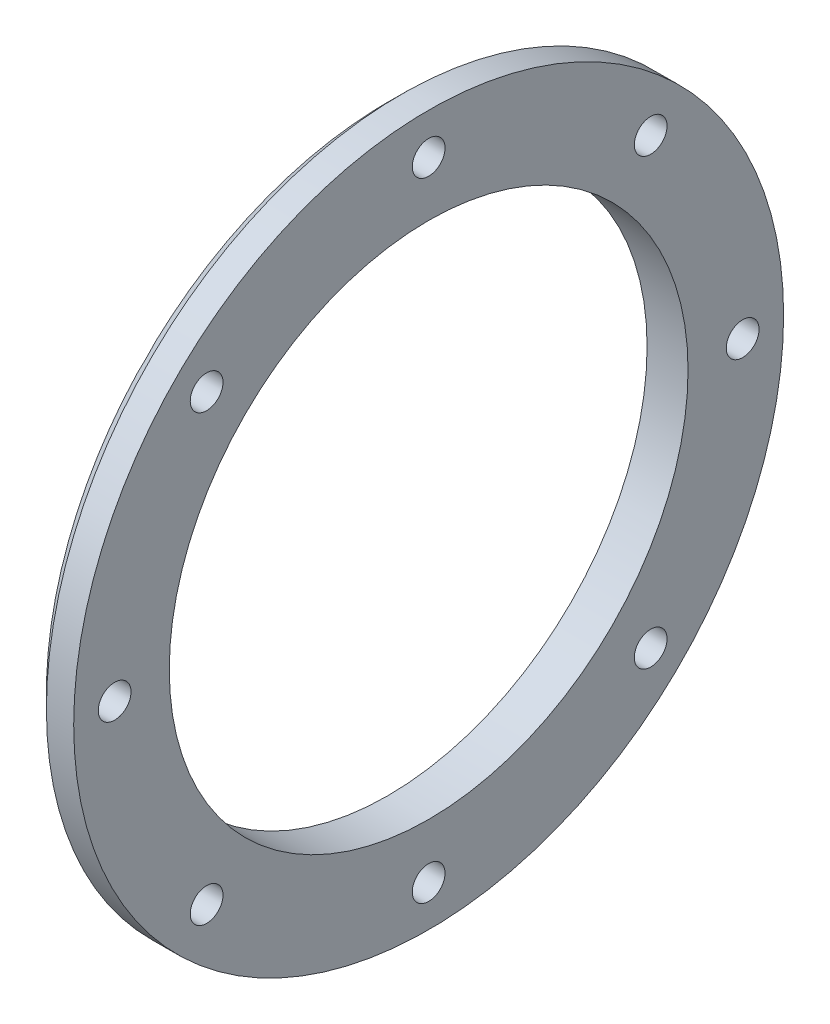
SolidWorks part; units mm, degrees
material "ABS"
ref_plane "Спереди" through (0, 0, 0) normal (0, 0, 1) x (1, 0, 0)
ref_plane "Сверху" through (0, 0, 0) normal (0, 1, 0) x (1, 0, 0)
ref_plane "Справа" through (0, 0, 0) normal (1, 0, 0) x (0, 0, -1)
sketch "Эскиз1" plane through (0, 0, 0) normal (0, 0, 1) x (1, 0, 0)
  line L5 (0, 19) -> (0, 25)
  line L6 (0, 25) -> (1, 26)
  line L7 (1, 26) -> (3, 26)
  line L8 (3, 26) -> (3, 19)
  line L9 (3, 19) -> (0, 19)
  line L10 (0, 0) -> (0, 19) construction
  line L11 (0, 0) -> (16163.9124, 0) construction
  point P7 (1.5, 19)
  dimension "D1" = 52
  dimension "D2" = 3
  dimension "D3" = 1
  dimension "D4" = 45
  dimension "D5" = 38
revolve "Повернуть1" add sketch "Эскиз1" angle 360 about L11
hole_wizard "Зенковка для винта с потайной головкой M21" positions "Эскиз2" profile "Эскиз3" countersink size "M2" standard "HASCO Metric" end condition through all
sketch "Эскиз2" plane through (0, 0, 0) normal (-1, 0, 0) x (0, 0, 1)
  line L0 (0, 0) -> (23, 0) construction
  line L2 (0, 0) -> (16.2635, 16.2635) construction
  circle A0 centre (0, 0) radius 23 construction
  point P0 (16.2635, 16.2635)
  dimension "D1" = 46
  dimension "D2" = 45
sketch "Эскиз3" plane through (0, 16.2635, 16.2635) normal (0, 1, 0) x (0, 0, 1)
  line L0 (0, 0) -> (0, 3)
  line L1 (0, 3) -> (1.2, 3)
  line L2 (1.2, 3) -> (1.2, 1)
  line L3 (1.2, 1) -> (2.2, 0)
  line L5 (2.2, 0) -> (0, 0)
  line L6 (-1.2, 1) -> (-2.2, 0) construction
  line L11 (0, -6.35) -> (0, 107.95) construction
  dimension "Диаметр сквозного отверстия" = 2.4
  dimension "Глубина сквозного отверстия" = 3
  dimension "Диаметр передней зенковки" = 4.4
  dimension "Угол передней зенковки" = 90
pattern_circular "Круговой массив1" count 8 over 360 about axis through (0, 0, 0) along (1, 0, 0) of "Зенковка для винта с потайной головкой M21"
